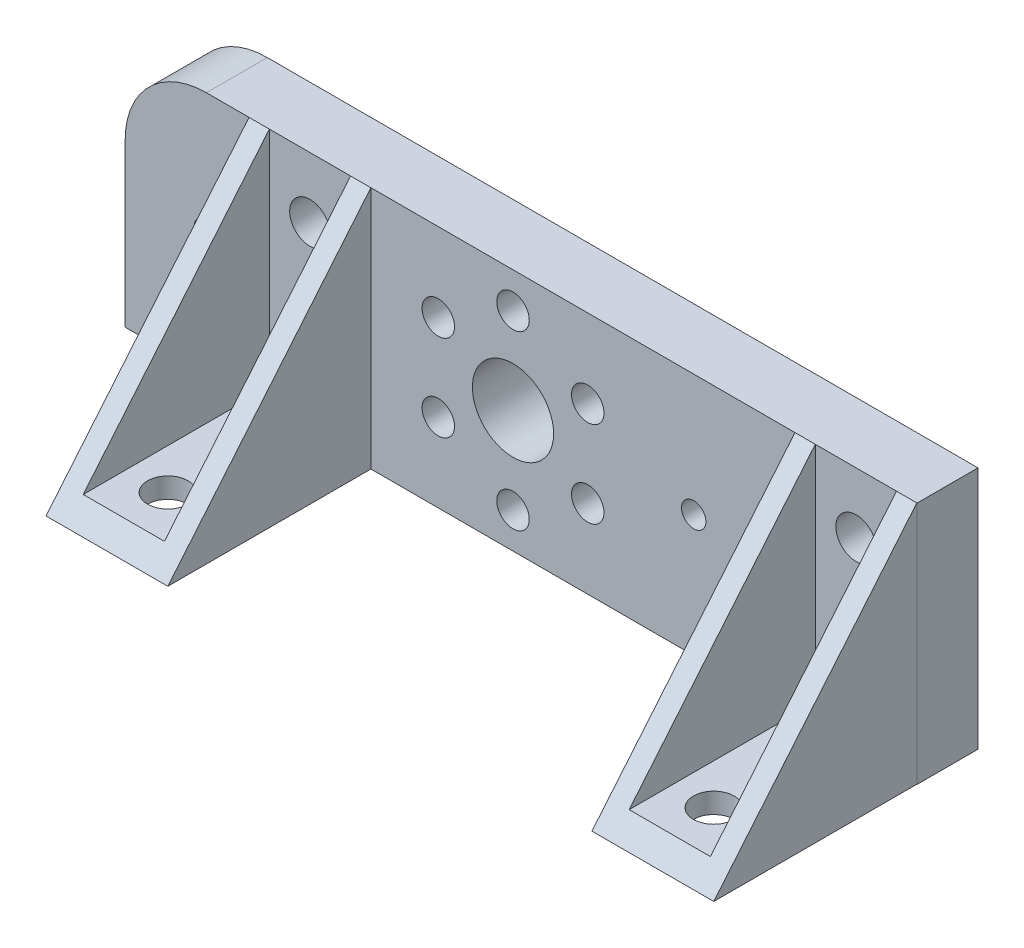
SolidWorks part; units mm, degrees
ref_plane "Front Plane" through (0, 0, 0) normal (0, 0, 1) x (1, 0, 0)
ref_plane "Top Plane" through (0, 0, 0) normal (0, 1, 0) x (1, 0, 0)
ref_plane "Right Plane" through (0, 0, 0) normal (1, 0, 0) x (0, 0, -1)
sketch "Sketch1" plane through (0, 0, 0) normal (0, 0, 1) x (1, 0, 0)
  line L0 (-23.1, 0) -> (15.9, 0) construction
  line L1 (-23.1, -6) -> (15.9, -6)
  line L2 (-23.1, -6) -> (-23.1, 2)
  line L3 (-19.1, 6) -> (15.9, 6)
  line L4 (15.9, -6) -> (15.9, 6)
  line L5 (12.9, -6) -> (12.9, 6.9573) construction
  line L6 (-14, -6) -> (-14, 8.3224) construction
  line L7 (-23.1, -3) -> (15.9, -3) construction
  line L8 (-22.973, 3) -> (15.773, 3) construction
  circle A0 centre (-4, 0) radius 2
  circle A1 centre (4.9, 0) radius 0.6
  arc A3 (-23.1, 2) -> (-19.1, 6) centre (-19.1, 2) cw
  circle A4 centre (-19.1, 0) radius 0.6
  circle A5 centre (12.9, 3) radius 1
  circle A6 centre (12.9, -3) radius 1
  circle A7 centre (-14, -3) radius 1
  circle A8 centre (-14, 3) radius 1
  point P0 (0, 0)
  point P34 (4.9, -6)
  point P39 (-19.1, -6)
  dimension "D1" = 8.9
  dimension "D2" = 1.2
  dimension "D3" = 4
  dimension "D6" = 4
  dimension "D8" = 11
  dimension "D4" = 24
  dimension "D5" = 4
  dimension "D11" = 1.2
  dimension "D16" = 2
  dimension "D17" = 2
  dimension "D18" = 2
  dimension "D19" = 2
  dimension "D9" = 12
  dimension "D10" = 6
  dimension "D12" = 10
  dimension "D13" = 3
  dimension "D14" = 3
  dimension "D15" = 3
extrude "Boss-Extrude1" add sketch "Sketch1" along normal blind 3
sketch "Sketch2" plane through (0, 0, 0) normal (0, 0, 1) x (1, 0, 0)
  circle A0 centre (4.9, 0) radius 0.75
  circle A1 centre (4.9, 0) radius 2.75
  dimension "D1" = 2
extrude "Boss-Extrude2" [suppressed] add sketch "Sketch2" along normal blind 1
sketch "Sketch3" plane through (0, 0, 3) normal (0, 0, 1) x (1, 0, 0)
  circle A0 centre (-4, 0) radius 4.25
  circle A1 centre (-4, 4.25) radius 0.8
  dimension "D1" = 8.5
  dimension "D2" = 1.6
extrude "Cut-Extrude1" cut sketch "Sketch3" against normal blind 3 contours A0 A1 | A0 A1
pattern_circular "CirPattern1" count 6 over 360 about axis through (-4, 0, 0) along (0, 0, 1) of "Cut-Extrude1"
sketch "Sketch4" plane through (0, 0, 3) normal (0, 0, 1) x (1, 0, 0)
  line L0 (-19.1, 6) -> (15.9, 6) construction
  line L1 (-17, -6) -> (-11, -6)
  line L2 (-17, -6) -> (-17, 6)
  line L3 (-17, 6) -> (-11, 6)
  line L4 (-11, -6) -> (-11, 6)
  line L5 (-17, -6) -> (-11, 6) construction
  line L6 (-17, 6) -> (-11, -6) construction
  line L7 (-14, 3) -> (-14, -7.6746) construction
  line L9 (-16, 6) -> (-16, -5)
  line L10 (-16, -5) -> (-12, -5)
  line L11 (-12, 6) -> (-12, -5)
  line L12 (-23.1, -6) -> (15.9, -6) construction
  point P0 (-14, 0)
  point P7 (-14, 0)
  line M28 (-23.1, -6) -> (15.9, -6)
  line M37 (15.9, 6) -> (-19.1, 6)
  dimension "D1" = 1
  dimension "D2" = 1
  dimension "D3" = 1
  dimension "D4" = 4
extrude "Boss-Extrude3" add sketch "Sketch4" along normal blind 10 contours L11 L10 L9 L3 L2 L4 M37 M28
sketch "Sketch5" plane through (-17, 0, 0) normal (-1, 0, 0) x (0, 0, 1)
  line L0 (3, 6) -> (13, -6)
  line L1 (13, -6) -> (13, 6)
  line L2 (13, 6) -> (3, 6)
extrude "Cut-Extrude2" cut sketch "Sketch5" against normal blind 45
sketch "Sketch6" plane through (0, 0, 3) normal (0, 0, 1) x (1, 0, 0)
  line L0 (-4, 0) -> (-4, 13.3198) construction
ref_plane "Plane1" through (-4, 0, 0) normal (1, 0, 0) x (0, 0, -1)
sketch "Sketch7" plane through (0, -5, 0) normal (0, 1, 0) x (1, 0, 0)
  line L0 (-14, -3) -> (-14, -13.6548) construction
  line L1 (-16, -3) -> (-12, -3) construction
  circle A0 centre (-14, -5) radius 1
  circle A1 centre (-14, -10) radius 1
  dimension "D1" = 2
  dimension "D2" = 2
  dimension "D3" = 2
  dimension "D4" = 5
extrude "Cut-Extrude3" cut sketch "Sketch7" against normal blind 10
pattern_linear "LPattern1" count 2 spacing 26.8868 along (1, 0, 0) of "Boss-Extrude3", "Cut-Extrude2", "Cut-Extrude3"
